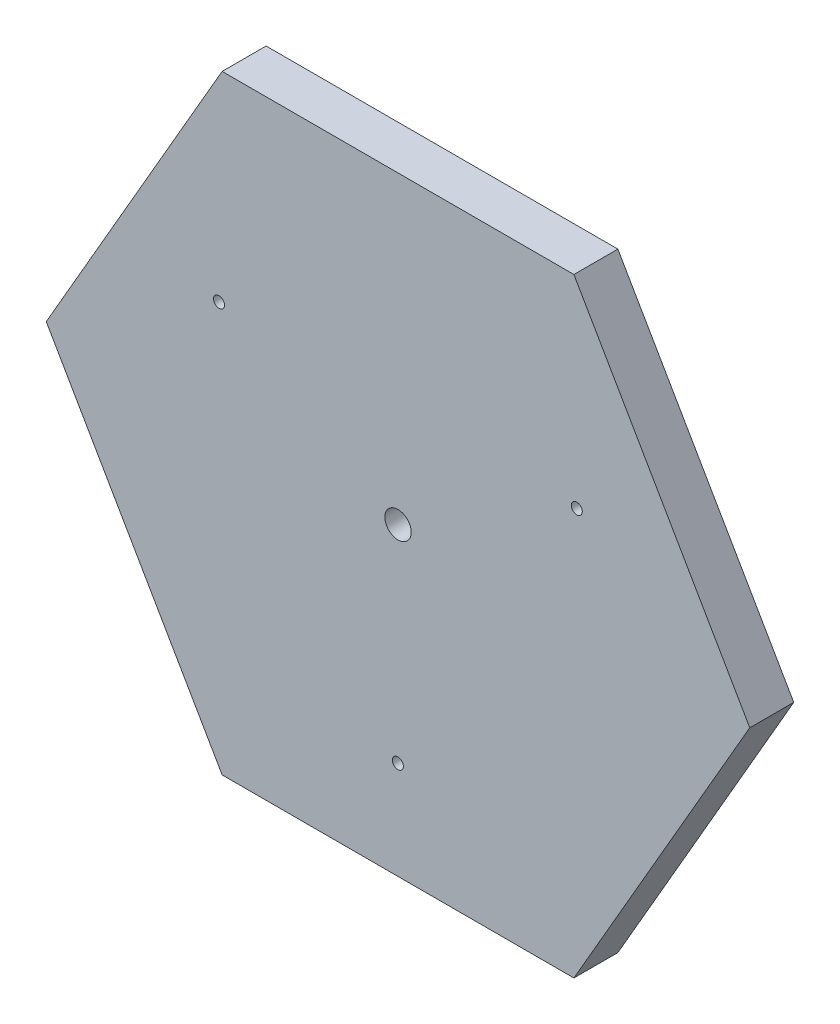
SolidWorks part; units mm, degrees
ref_plane "Plano frontal" through (0, 0, 0) normal (0, 0, 1) x (1, 0, 0)
ref_plane "Plano superior" through (0, 0, 0) normal (0, 1, 0) x (1, 0, 0)
ref_plane "Plano direito" through (0, 0, 0) normal (1, 0, 0) x (0, 0, -1)
sketch "Model" plane through (0, 0, 0) normal (0, 0, 1) x (1, 0, 0)
  line L0 (24.5383, 125.5364) -> (-15.4617, 56.2544)
  line L1 (-15.4617, 56.2544) -> (24.5383, -13.0277)
  line L2 (24.5383, -13.0277) -> (104.5383, -13.0277)
  line L3 (104.5383, -13.0277) -> (144.5383, 56.2544)
  line L4 (144.5383, 56.2544) -> (104.5383, 125.5364)
  line L5 (104.5383, 125.5364) -> (24.5383, 125.5364)
  circle A0 centre (23.8298, 79.7598) radius 1.25
  circle A1 centre (64.5, 9.2544) radius 1.25
  circle A2 centre (105.195, 79.7661) radius 1.25
  circle A3 centre (64.5383, 56.2544) radius 3
  dimension "D1" = 160
  dimension "D2" = 81.3652
  dimension "D3" = 81.4124
sketch "Esboço1" plane through (0, 0, 0) normal (0, 0, 1) x (1, 0, 0)
  line L0 (24.5383, 125.5364) -> (-15.4617, 56.2544)
  line L1 (-15.4617, 56.2544) -> (24.5383, -13.0277)
  line L2 (24.5383, -13.0277) -> (104.5383, -13.0277)
  line L3 (104.5383, -13.0277) -> (144.5383, 56.2544)
  line L4 (144.5383, 56.2544) -> (104.5383, 125.5364)
  line L5 (104.5383, 125.5364) -> (24.5383, 125.5364)
  circle A0 centre (23.8298, 79.7598) radius 1.25
  circle A1 centre (64.5, 9.2544) radius 1.25
  circle A2 centre (105.195, 79.7661) radius 1.25
  circle A3 centre (64.5383, 56.2544) radius 3
  dimension "D1" = 160
  dimension "D2" = 81.3652
  dimension "D3" = 81.4124
extrude "Ressalto-extrusão1" add sketch "Esboço1" along normal blind 10
